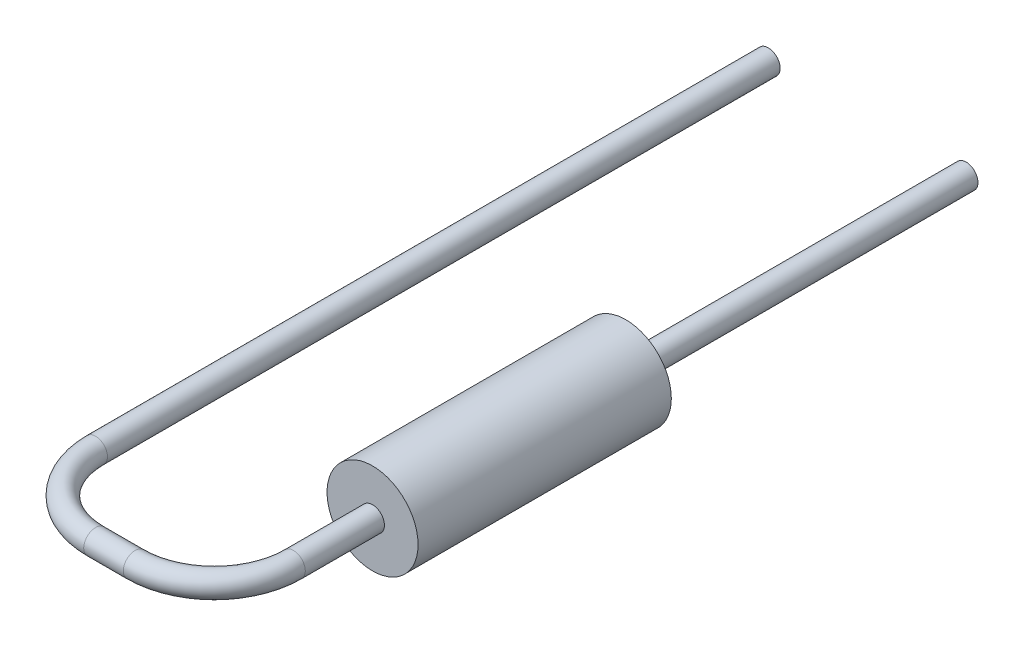
SolidWorks part; units mm, degrees
ref_plane "Front Plane" through (0, 0, 0) normal (0, 0, 1) x (1, 0, 0)
ref_plane "Top Plane" through (0, 0, 0) normal (0, 1, 0) x (1, 0, 0)
ref_plane "Right Plane" through (0, 0, 0) normal (1, 0, 0) x (0, 0, -1)
sketch "Sketch2" plane through (0, 0, 0) normal (0, 0, 1) x (1, 0, 0)
  circle A0 centre (0, 0) radius 1.15
  dimension "D1" = 2.3
extrude "Resistor Body" add sketch "Sketch2" along normal blind 6.4
sketch "Lead1 Path" plane through (0, 0, 0) normal (0, -1, 0) x (-1, 0, 0)
  line L1 (-1.15, -6.4) -> (1.15, -6.4) construction
  line L2 (0, -6.4) -> (0, 0) construction
  line L3 (0, -6.4) -> (0, -8.4)
  line L4 (5, -8.4) -> (5, 8.6)
  line L5 (2, -10.4) -> (3, -10.4)
  arc A0 (5, -8.4) -> (3, -10.4) centre (3, -8.4) cw
  arc A1 (0, -8.4) -> (2, -10.4) centre (2, -8.4) ccw
  point P11 (0, -10.4)
  point P14 (5, -10.4)
  dimension "D4" = 2
  dimension "D1" = 19
  dimension "D2" = 4
  dimension "D3" = 5
sketch "Lead1 Profile" plane through (0, 0, 6.4) normal (0, 0, 1) x (-1, 0, 0)
  circle A0 centre (0, 0) radius 0.3
  dimension "D1" = 0.6
sweep "Lead1" add profiles "Lead1 Profile" path "Lead1 Path"
sketch "Sketch6" plane through (0, 0, 0) normal (0, 0, -1) x (1, 0, 0)
  circle A0 centre (0, 0) radius 0.3 construction
  circle A1 centre (0, 0) radius 0.3
extrude "Lead2" add sketch "Sketch6" along normal up to surface (8.6 mm away) up to face at (-5.3, 0, -8.6)
ref_plane "Mounting Plane" through (0, 0, -5.5) normal (0, 0, 1) x (1, 0, 0)
sketch "Component_Outline" plane through (0, 0, -5.5) normal (0, 0, 1) x (1, 0, 0)
  line L0 (-1.1102, 0.3) -> (-5, 0.3)
  line L1 (0, 0.3) -> (-2, 0.3) construction
  line L2 (-3, 0.3) -> (-5, 0.3) construction
  line L3 (-5, -0.3) -> (-1.1102, -0.3)
  line L4 (-2, -0.3) -> (0, -0.3) construction
  arc A0 (-1.1102, -0.3) -> (-1.1102, 0.3) centre (0, 0) ccw
  circle A1 centre (-5, 0) radius 0.3 construction
  arc A2 (-5, 0.3) -> (-5, -0.3) centre (-5, 0) ccw
  dimension "D1" = 1.15
